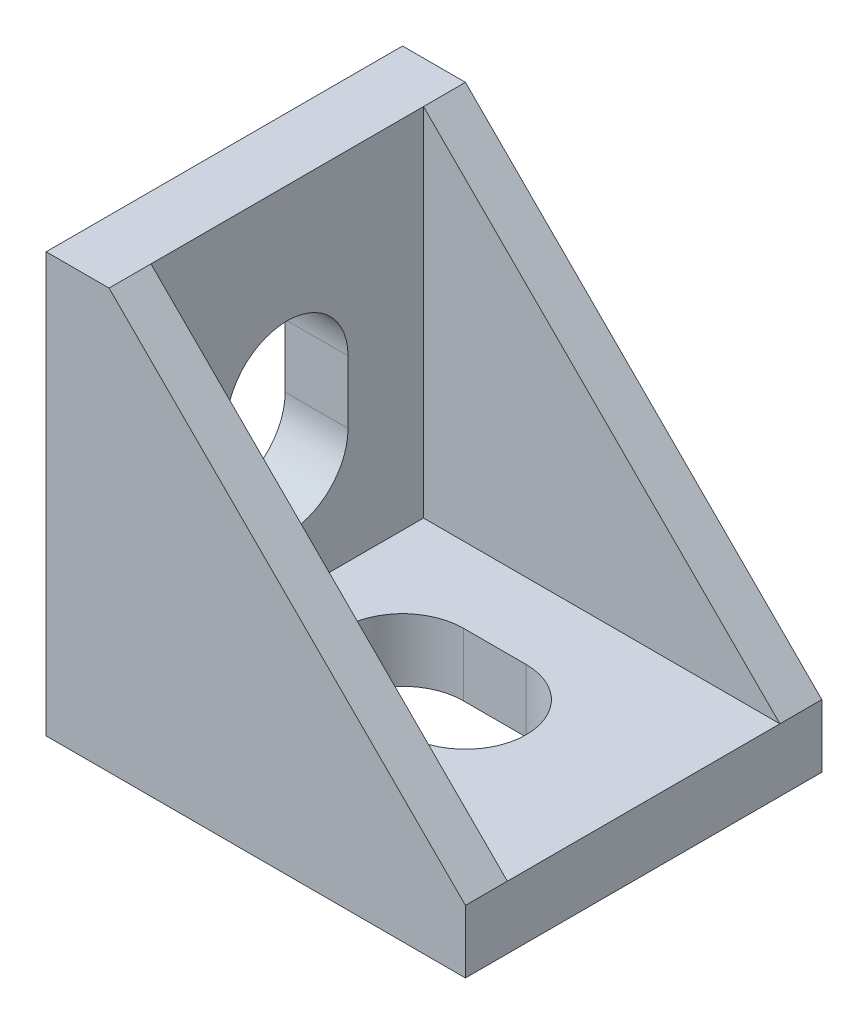
SolidWorks part; units mm, degrees
material "6061-T6 (SS)"
ref_plane "Front Plane" through (0, 0, 0) normal (0, 0, 1) x (1, 0, 0)
ref_plane "Top Plane" through (0, 0, 0) normal (0, 1, 0) x (1, 0, 0)
ref_plane "Right Plane" through (0, 0, 0) normal (1, 0, 0) x (0, 0, -1)
sketch "Sketch1" plane through (0, 0, 0) normal (0, 0, 1) x (1, 0, 0)
  line L0 (0, 20) -> (0, 0)
  line L1 (0, 0) -> (20, 0)
  line L2 (20, 0) -> (20, 3)
  line L3 (20, 3) -> (3, 20)
  line L4 (3, 20) -> (0, 20)
  line L5 (0, 0) -> (11.5, 11.5) construction
  dimension "D1" = 20
  dimension "D3" = 3
extrude "Boss-Extrude1" add sketch "Sketch1" along normal mid plane 17
sketch "Sketch2" plane through (0, 20, 0) normal (0, 1, 0) x (1, 0, 0)
  line L0 (3, -8.5) -> (3, 8.5) construction
  line L1 (3, 6.5) -> (20, 6.5)
  line L2 (3, 6.5) -> (3, -6.5)
  line L3 (3, -6.5) -> (20, -6.5)
  line L4 (20, 6.5) -> (20, -6.5)
  line L5 (20, -8.5) -> (20, 8.5) construction
  line L6 (20, 8.5) -> (3, 8.5) construction
  line L7 (3, 0) -> (0, 0) construction
  dimension "D1" = 2
extrude "Cut-Extrude1" cut sketch "Sketch2" against normal blind 17
sketch "Sketch3" plane through (3, 0, 0) normal (1, 0, 0) x (0, 0, -1)
  line L0 (0, 20) -> (0, 10) construction
  line L1 (6.5, 20) -> (-6.5, 20) construction
  line L2 (0, 8.5) -> (0, 11.5) construction
  line L3 (-2.9, 8.5) -> (-2.9, 11.5)
  line L4 (2.9, 8.5) -> (2.9, 11.5)
  line L5 (-8.5, 0) -> (8.5, 0) construction
  arc A0 (-2.9, 8.5) -> (2.9, 8.5) centre (0, 8.5) ccw
  arc A1 (2.9, 11.5) -> (-2.9, 11.5) centre (0, 11.5) ccw
  point P7 (0, 10)
  dimension "D1" = 5.8
  dimension "D2" = 3
  dimension "D3" = 8.5
extrude "Cut-Extrude2" cut sketch "Sketch3" against normal up to next
sketch "Sketch5" plane through (0, 3, 0) normal (0, 1, 0) x (1, 0, 0)
  line L0 (20, 0) -> (10, 0) construction
  line L2 (20, -6.5) -> (20, 6.5) construction
  line L3 (11.5, 0) -> (8.5, 0) construction
  line L4 (11.5, -2.9) -> (8.5, -2.9)
  line L6 (11.5, 2.9) -> (8.5, 2.9)
  line L7 (0, -8.5) -> (0, 8.5) construction
  arc A0 (11.5, -2.9) -> (11.5, 2.9) centre (11.5, 0) ccw
  arc A1 (8.5, 2.9) -> (8.5, -2.9) centre (8.5, 0) ccw
  point P7 (10, 0)
  dimension "D1" = 5.8
  dimension "D2" = 3
  dimension "D3" = 8.5
extrude "Cut-Extrude3" cut sketch "Sketch5" against normal through all
sketch "Sketch6" plane through (0, 0, 0) normal (0, 0, 1) x (1, 0, 0)
  line L0 (0, 20) -> (0, 0) construction
  line L1 (0, 18.5) -> (-1, 18.5)
  line L2 (0, 18.5) -> (0, 16.65)
  line L3 (0, 16.65) -> (-1, 16.65)
  line L4 (-1, 18.5) -> (-1, 16.65)
  line L5 (0, 10) -> (-1.5249, 10) construction
  line L6 (-1, 1.5) -> (-1, 3.35)
  line L7 (0, 3.35) -> (-1, 3.35)
  line L8 (0, 1.5) -> (0, 3.35)
  line L9 (0, 1.5) -> (-1, 1.5)
  line L10 (0, 0) -> (6.9595, 6.9595) construction
  line L11 (0, 0) -> (20, 0) construction
  line L12 (1.5, 0) -> (1.5, -1)
  line L13 (1.5, 0) -> (3.35, 0)
  line L14 (3.35, 0) -> (3.35, -1)
  line L15 (1.5, -1) -> (3.35, -1)
  line L16 (18.5, -1) -> (16.65, -1)
  line L17 (16.65, 0) -> (16.65, -1)
  line L18 (18.5, 0) -> (16.65, 0)
  line L19 (18.5, 0) -> (18.5, -1)
  dimension "D1" = 45
  dimension "D2" = 1.85
  dimension "D3" = 1
  dimension "D4" = 17
extrude "Boss-Extrude2" add sketch "Sketch6" along normal mid plane 4
